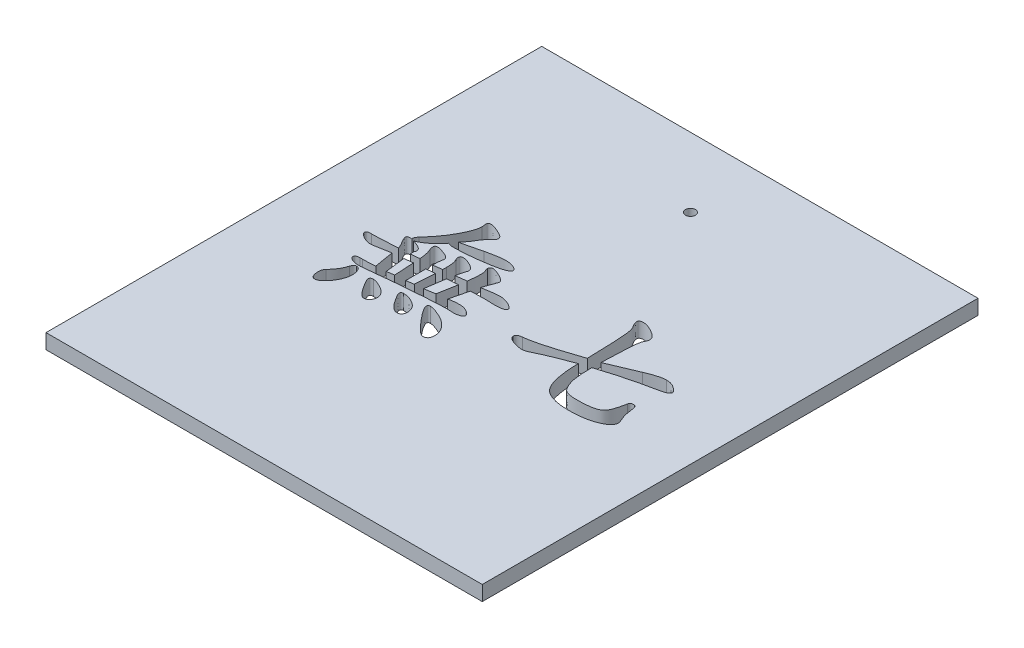
SolidWorks part; units mm, degrees
ref_plane "前视基准面" through (0, 0, 0) normal (0, 0, 1) x (1, 0, 0)
ref_plane "上视基准面" through (0, 0, 0) normal (0, 1, 0) x (1, 0, 0)
ref_plane "右视基准面" through (0, 0, 0) normal (1, 0, 0) x (0, 0, -1)
sketch "草图1" plane through (0, 0, 0) normal (0, 0, 1) x (1, 0, 0)
  line L0 (-36.2869, 30.617) -> (7.7131, 30.617)
  line L1 (7.7131, 30.617) -> (7.7131, 29.117)
  line L2 (7.7131, 29.117) -> (-36.2869, 29.117)
  line L3 (-36.2869, 29.117) -> (-36.2869, 30.617)
extrude "凸台-拉伸1" add sketch "草图1" along normal blind 50
ref_plane "基准面1" through (-14.2869, 0, 0) normal (1, 0, 0) x (0, 0, -1)
sketch "草图3" plane through (0, 30.617, 0) normal (0, 1, 0) x (1, 0, 0)
  text T0 "無七" font "华文楷体" height in points 36
extrude "切除-拉伸1" cut sketch "草图3" against normal blind 50
sketch "草图4" plane through (0, 30.617, 0) normal (0, 1, 0) x (1, 0, 0)
  line L0 (-14.2869, 0) -> (-14.2869, -7) construction
  line L1 (7.7131, 0) -> (-36.2869, 0) construction
  line L2 (-14.2869, -0.825) -> (-14.2869, 0.825) construction
  circle A0 centre (-14.2869, -7) radius 0.5
extrude "切除-拉伸2" cut sketch "草图4" against normal blind 1.5
